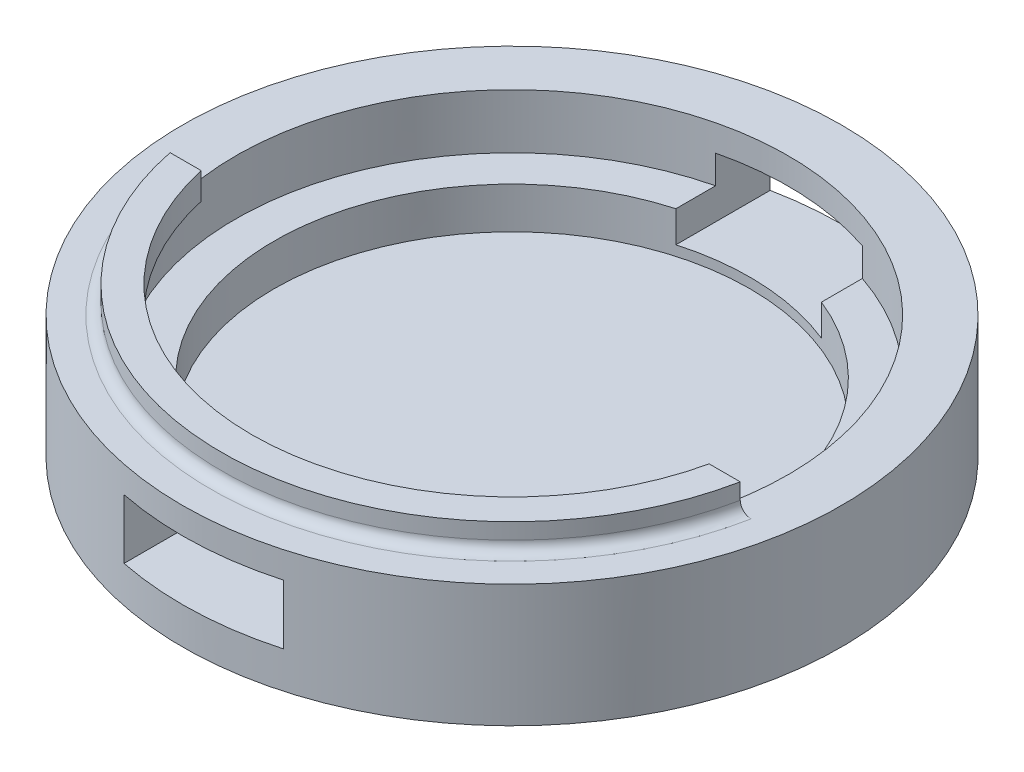
SolidWorks part; units mm, degrees
ref_plane "Alzado" through (0, 0, 0) normal (0, 0, 1) x (1, 0, 0)
ref_plane "Planta" through (0, 0, 0) normal (0, 1, 0) x (1, 0, 0)
ref_plane "Vista lateral" through (0, 0, 0) normal (1, 0, 0) x (0, 0, -1)
sketch "Croquis1" plane through (0, 0, 0) normal (0, 1, 0) x (1, 0, 0)
  circle A0 centre (0, 0) radius 51.815
  circle A1 centre (0, 0) radius 61.815
  dimension "D1" = 103.63
  dimension "D2" = 123.63
extrude "Saliente-Extruir2" add sketch "Croquis1" along normal blind 18
sketch "Croquis2" plane through (0, 18, 0) normal (0, 1, 0) x (1, 0, 0)
  line L0 (47.6484, -10.6642) -> (53.4742, -10.6642)
  line L1 (-53.4742, -10.6642) -> (-47.6484, -10.6642)
  arc A2 (-47.6484, -10.6642) -> (47.6484, -10.6642) centre (0, 0) ccw
  arc A3 (-53.4742, -10.6642) -> (53.4742, -10.6642) centre (0, 0) ccw
extrude "Saliente-Extruir4" add sketch "Croquis2" along normal blind 5
fillet "Redondeo2" radius 2 1 edges at (0, 18, 54.5272)
sketch "Croquis3" plane through (0, 0, 0) normal (0, -1, 0) x (1, 0, 0)
  circle A0 centre (0, 0) radius 61.815
extrude "Saliente-Extruir5" add sketch "Croquis3" along normal blind 5
sketch "Croquis4" plane through (0, -5, 0) normal (0, -1, 0) x (1, 0, 0)
  circle A0 centre (0, 55.6983) radius 3.5
  circle A1 centre (55.6983, 0) radius 3.5
  circle A2 centre (0, -55.6983) radius 3.5
  circle A3 centre (-55.6983, 0) radius 3.5
  point P11 (0, 0)
  dimension "D1" = 7
  dimension "D2" = 4
extrude "Cortar-Extruir1" cut sketch "Croquis4" against normal blind 5
sketch "Croquis5" plane through (0, -5, 0) normal (0, -1, 0) x (1, 0, 0)
  circle A0 centre (0, 55.6983) radius 3.5
  dimension "D1" = 55.6983
sketch "Croquis6" plane through (0, -5, 0) normal (0, -1, 0) x (1, 0, 0)
  arc A0 (-9.4545, -8.1769) -> (-8.1769, -9.4545) centre (0, 0) ccw
  spline S0 degree 3 poles (-10.111, 8.9914) (-14.9099, 15.405) (-3.1026, 26.7366) (26.6769, 28.6218) (9.3118, 18.3412) (8.6434, 12.2458) (8.9914, 10.111) knots 0.00619 0.00619 0.00619 0.00619 0.153841 0.345958 0.455748 0.513421 0.513421 0.513421 0.513421
  spline S1 degree 3 poles (8.9914, 10.111) (15.405, 14.9099) (26.7366, 3.1026) (28.6218, -26.6769) (18.3412, -9.3118) (12.2458, -8.6434) (10.111, -8.9914) knots 0.00619 0.00619 0.00619 0.00619 0.153841 0.345958 0.455748 0.513421 0.513421 0.513421 0.513421
  spline S2 degree 3 poles (10.111, -8.9914) (14.9099, -15.405) (3.1026, -26.7366) (-26.6769, -28.6218) (-9.3118, -18.3412) (-8.6434, -12.2458) (-8.9914, -10.111) knots 0.00619 0.00619 0.00619 0.00619 0.153841 0.345958 0.455748 0.513421 0.513421 0.513421 0.513421
  spline S3 degree 3 poles (-8.9914, -10.111) (-15.405, -14.9099) (-26.7366, -3.1026) (-28.6218, 26.6769) (-18.3412, 9.3118) (-12.2458, 8.6434) (-10.111, 8.9914) knots 0.00619 0.00619 0.00619 0.00619 0.153841 0.345958 0.455748 0.513421 0.513421 0.513421 0.513421
  point P25 (0, 0)
  dimension "D1" = 25
extrude "Cortar-Extruir2" cut sketch "Croquis6" against normal blind 3
sketch "Croquis7" plane through (0, -5, 0) normal (0, -1, 0) x (1, 0, 0)
  spline S14 degree 3 poles (340.8778, 2969.6757) (-144.0274, -413.7995) (-31.7257, 0.5508) (14.063, -10.1213) (14.3721, -10.2142) (14.9734, -10.4385) (15.2642, -10.5689) (15.8271, -10.8641) (16.0991, -11.0293) (16.6282, -11.3869) (16.8864, -11.5796) (17.6344, -12.1796) (18.1019, -12.6098) (19.4549, -13.9486) (20.2891, -14.907) (21.5423, -16.3427) (21.9597, -16.8217) (22.609, -17.5175) (22.8295, -17.7456) (23.2877, -18.1844) (23.5242, -18.3947) (24.0303, -18.7738) (24.3032, -18.9445) (24.7448, -19.1186) (24.8999, -19.1634) (25.2114, -19.2156) (25.3683, -19.2238) (25.6844, -19.1998) (25.8426, -19.1669) (26.1406, -19.0631) (26.2849, -18.9906) (26.6815, -18.7261) (26.9002, -18.4852) (27.2432, -17.9553) (27.3735, -17.6609) (27.5773, -17.0645) (27.6528, -16.7587) (27.7725, -16.1379) (27.8161, -15.8239) (27.8811, -15.1989) (27.9026, -14.8864) (27.9436, -13.9493) (27.94, -13.3248) (27.8935, -12.0761) (27.8501, -11.4519) (27.7324, -10.2038) (27.658, -9.5793) (27.4843, -8.3403) (27.3849, -7.7245) (27.0528, -5.8869) (26.787, -4.6749) (26.1706, -2.2757) (25.82, -1.0886) (25.0229, 1.2577) (24.5768, 2.4168) (23.8133, 4.1279) (23.5428, 4.6936) (22.9629, 5.8135) (22.6552, 6.3641) (21.9988, 7.4376) (21.6498, 7.9614) (20.8983, 8.9751) (20.4973, 9.4626) (19.6398, 10.376) (19.1824, 10.8036) (18.438, 11.3857) (18.1786, 11.5706) (17.6463, 11.9104) (17.3729, 12.0658) (16.8103, 12.3447) (16.5211, 12.4681) (15.9247, 12.6788) (15.6173, 12.7658) (14.695, 12.9611) (14.0708, 13.0077) (13.1203, 12.9496) (12.8053, 12.9089) (12.1872, 12.7898) (11.8826, 12.7113) (11.2815, 12.52) (10.984, 12.4066) (-24.7173, -3.2736) (39.5362, -229.2031) (-1376.9054, 2670.394) knots -2.259503 -2.259503 -2.259503 -2.259503 0.03125 0.03125 0.046875 0.046875 0.0625 0.0625 0.078125 0.078125 0.09375 0.09375 0.125 0.125 0.1875 0.1875 0.21875 0.21875 0.234375 0.234375 0.25 0.25 0.265625 0.265625 0.273437 0.273437 0.28125 0.28125 0.289062 0.289062 0.296875 0.296875 0.3125 0.3125 0.328125 0.328125 0.34375 0.34375 0.359375 0.359375 0.375 0.375 0.40625 0.40625 0.4375 0.4375 0.46875 0.46875 0.5 0.5 0.5625 0.5625 0.625 0.625 0.6875 0.6875 0.71875 0.71875 0.75 0.75 0.78125 0.78125 0.8125 0.8125 0.84375 0.84375 0.859375 0.859375 0.875 0.875 0.890625 0.890625 0.90625 0.90625 0.9375 0.9375 0.953125 0.953125 0.96875 0.96875 0.984375 0.984375 2.889942 2.889942 2.889942 2.889942 only from (11.8559, -9.8418) to (9.8418, 11.8559)
  spline S15 degree 3 poles (-2969.6829, 340.8787) (413.7996, -144.0274) (-0.5508, -31.7257) (10.1213, 14.063) (10.2142, 14.3721) (10.4385, 14.9734) (10.5689, 15.2642) (10.8641, 15.8271) (11.0293, 16.0991) (11.3869, 16.6282) (11.5796, 16.8864) (12.1796, 17.6344) (12.6098, 18.1019) (13.9486, 19.4549) (14.907, 20.2891) (16.3427, 21.5423) (16.8217, 21.9597) (17.5175, 22.609) (17.7456, 22.8295) (18.1844, 23.2877) (18.3947, 23.5242) (18.7738, 24.0303) (18.9445, 24.3032) (19.1186, 24.7448) (19.1634, 24.8999) (19.2156, 25.2114) (19.2238, 25.3683) (19.1998, 25.6844) (19.1669, 25.8426) (19.0631, 26.1406) (18.9906, 26.2849) (18.7261, 26.6815) (18.4852, 26.9002) (17.9553, 27.2432) (17.6609, 27.3735) (17.0645, 27.5773) (16.7587, 27.6528) (16.1379, 27.7725) (15.8239, 27.8161) (15.1989, 27.8811) (14.8864, 27.9026) (13.9493, 27.9436) (13.3248, 27.94) (12.0761, 27.8935) (11.4519, 27.8501) (10.2038, 27.7324) (9.5793, 27.658) (8.3403, 27.4843) (7.7245, 27.3849) (5.8869, 27.0528) (4.6749, 26.787) (2.2757, 26.1706) (1.0886, 25.82) (-1.2577, 25.0229) (-2.4168, 24.5768) (-4.1279, 23.8133) (-4.6936, 23.5428) (-5.8135, 22.9629) (-6.3641, 22.6552) (-7.4376, 21.9988) (-7.9614, 21.6498) (-8.9751, 20.8983) (-9.4626, 20.4973) (-10.376, 19.6398) (-10.8036, 19.1824) (-11.3857, 18.438) (-11.5706, 18.1786) (-11.9104, 17.6463) (-12.0658, 17.3729) (-12.3447, 16.8103) (-12.4681, 16.5211) (-12.6788, 15.9247) (-12.7658, 15.6173) (-12.9611, 14.695) (-13.0077, 14.0708) (-12.9496, 13.1203) (-12.9089, 12.8053) (-12.7898, 12.1872) (-12.7113, 11.8826) (-12.52, 11.2815) (-12.4066, 10.984) (3.2736, -24.7173) (229.2031, 39.5362) (-2670.3929, -1376.9044) knots -2.259503 -2.259503 -2.259503 -2.259503 0.03125 0.03125 0.046875 0.046875 0.0625 0.0625 0.078125 0.078125 0.09375 0.09375 0.125 0.125 0.1875 0.1875 0.21875 0.21875 0.234375 0.234375 0.25 0.25 0.265625 0.265625 0.273437 0.273437 0.28125 0.28125 0.289062 0.289062 0.296875 0.296875 0.3125 0.3125 0.328125 0.328125 0.34375 0.34375 0.359375 0.359375 0.375 0.375 0.40625 0.40625 0.4375 0.4375 0.46875 0.46875 0.5 0.5 0.5625 0.5625 0.625 0.625 0.6875 0.6875 0.71875 0.71875 0.75 0.75 0.78125 0.78125 0.8125 0.8125 0.84375 0.84375 0.859375 0.859375 0.875 0.875 0.890625 0.890625 0.90625 0.90625 0.9375 0.9375 0.953125 0.953125 0.96875 0.96875 0.984375 0.984375 2.889942 2.889942 2.889942 2.889942 only from (9.8418, 11.8559) to (-11.8559, 9.8418)
  spline S16 degree 3 poles (-340.8778, -2969.6757) (144.0274, 413.7995) (31.7257, -0.5508) (-14.063, 10.1213) (-14.3721, 10.2142) (-14.9734, 10.4385) (-15.2642, 10.5689) (-15.8271, 10.8641) (-16.0991, 11.0293) (-16.6282, 11.3869) (-16.8864, 11.5796) (-17.6344, 12.1796) (-18.1019, 12.6098) (-19.4549, 13.9486) (-20.2891, 14.907) (-21.5423, 16.3427) (-21.9597, 16.8217) (-22.609, 17.5175) (-22.8295, 17.7456) (-23.2877, 18.1844) (-23.5242, 18.3947) (-24.0303, 18.7738) (-24.3032, 18.9445) (-24.7448, 19.1186) (-24.8999, 19.1634) (-25.2114, 19.2156) (-25.3683, 19.2238) (-25.6844, 19.1998) (-25.8426, 19.1669) (-26.1406, 19.0631) (-26.2849, 18.9906) (-26.6815, 18.7261) (-26.9002, 18.4852) (-27.2432, 17.9553) (-27.3735, 17.6609) (-27.5773, 17.0645) (-27.6528, 16.7587) (-27.7725, 16.1379) (-27.8161, 15.8239) (-27.8811, 15.1989) (-27.9026, 14.8864) (-27.9436, 13.9493) (-27.94, 13.3248) (-27.8935, 12.0761) (-27.8501, 11.4519) (-27.7324, 10.2038) (-27.658, 9.5793) (-27.4843, 8.3403) (-27.3849, 7.7245) (-27.0528, 5.8869) (-26.787, 4.6749) (-26.1706, 2.2757) (-25.82, 1.0886) (-25.0229, -1.2577) (-24.5768, -2.4168) (-23.8133, -4.1279) (-23.5428, -4.6936) (-22.9629, -5.8135) (-22.6552, -6.3641) (-21.9988, -7.4376) (-21.6498, -7.9614) (-20.8983, -8.9751) (-20.4973, -9.4626) (-19.6398, -10.376) (-19.1824, -10.8036) (-18.438, -11.3857) (-18.1786, -11.5706) (-17.6463, -11.9104) (-17.3729, -12.0658) (-16.8103, -12.3447) (-16.5211, -12.4681) (-15.9247, -12.6788) (-15.6173, -12.7658) (-14.695, -12.9611) (-14.0708, -13.0077) (-13.1203, -12.9496) (-12.8053, -12.9089) (-12.1872, -12.7898) (-11.8826, -12.7113) (-11.2815, -12.52) (-10.984, -12.4066) (24.7173, 3.2736) (-39.5362, 229.2031) (1376.9054, -2670.3939) knots -2.259503 -2.259503 -2.259503 -2.259503 0.03125 0.03125 0.046875 0.046875 0.0625 0.0625 0.078125 0.078125 0.09375 0.09375 0.125 0.125 0.1875 0.1875 0.21875 0.21875 0.234375 0.234375 0.25 0.25 0.265625 0.265625 0.273437 0.273437 0.28125 0.28125 0.289062 0.289062 0.296875 0.296875 0.3125 0.3125 0.328125 0.328125 0.34375 0.34375 0.359375 0.359375 0.375 0.375 0.40625 0.40625 0.4375 0.4375 0.46875 0.46875 0.5 0.5 0.5625 0.5625 0.625 0.625 0.6875 0.6875 0.71875 0.71875 0.75 0.75 0.78125 0.78125 0.8125 0.8125 0.84375 0.84375 0.859375 0.859375 0.875 0.875 0.890625 0.890625 0.90625 0.90625 0.9375 0.9375 0.953125 0.953125 0.96875 0.96875 0.984375 0.984375 2.889942 2.889942 2.889942 2.889942 only from (-11.8559, 9.8418) to (-9.8418, -11.8559)
  spline S17 degree 3 poles (2969.6829, -340.8787) (-413.7996, 144.0274) (0.5508, 31.7257) (-10.1213, -14.063) (-10.2142, -14.3721) (-10.4385, -14.9734) (-10.5689, -15.2642) (-10.8641, -15.8271) (-11.0293, -16.0991) (-11.3869, -16.6282) (-11.5796, -16.8864) (-12.1796, -17.6344) (-12.6098, -18.1019) (-13.9486, -19.4549) (-14.907, -20.2891) (-16.3427, -21.5423) (-16.8217, -21.9597) (-17.5175, -22.609) (-17.7456, -22.8295) (-18.1844, -23.2877) (-18.3947, -23.5242) (-18.7738, -24.0303) (-18.9445, -24.3032) (-19.1186, -24.7448) (-19.1634, -24.8999) (-19.2156, -25.2114) (-19.2238, -25.3683) (-19.1998, -25.6844) (-19.1669, -25.8426) (-19.0631, -26.1406) (-18.9906, -26.2849) (-18.7261, -26.6815) (-18.4852, -26.9002) (-17.9553, -27.2432) (-17.6609, -27.3735) (-17.0645, -27.5773) (-16.7587, -27.6528) (-16.1379, -27.7725) (-15.8239, -27.8161) (-15.1989, -27.8811) (-14.8864, -27.9026) (-13.9493, -27.9436) (-13.3248, -27.94) (-12.0761, -27.8935) (-11.4519, -27.8501) (-10.2038, -27.7324) (-9.5793, -27.658) (-8.3403, -27.4843) (-7.7245, -27.3849) (-5.8869, -27.0528) (-4.6749, -26.787) (-2.2757, -26.1706) (-1.0886, -25.82) (1.2577, -25.0229) (2.4168, -24.5768) (4.1279, -23.8133) (4.6936, -23.5428) (5.8135, -22.9629) (6.3641, -22.6552) (7.4376, -21.9988) (7.9614, -21.6498) (8.9751, -20.8983) (9.4626, -20.4973) (10.376, -19.6398) (10.8036, -19.1824) (11.3857, -18.438) (11.5706, -18.1786) (11.9104, -17.6463) (12.0658, -17.3729) (12.3447, -16.8103) (12.4681, -16.5211) (12.6788, -15.9247) (12.7658, -15.6173) (12.9611, -14.695) (13.0077, -14.0708) (12.9496, -13.1203) (12.9089, -12.8053) (12.7898, -12.1872) (12.7113, -11.8826) (12.52, -11.2815) (12.4066, -10.984) (-3.2736, 24.7173) (-229.2031, -39.5362) (2670.393, 1376.9044) knots -2.259503 -2.259503 -2.259503 -2.259503 0.03125 0.03125 0.046875 0.046875 0.0625 0.0625 0.078125 0.078125 0.09375 0.09375 0.125 0.125 0.1875 0.1875 0.21875 0.21875 0.234375 0.234375 0.25 0.25 0.265625 0.265625 0.273437 0.273437 0.28125 0.28125 0.289062 0.289062 0.296875 0.296875 0.3125 0.3125 0.328125 0.328125 0.34375 0.34375 0.359375 0.359375 0.375 0.375 0.40625 0.40625 0.4375 0.4375 0.46875 0.46875 0.5 0.5 0.5625 0.5625 0.625 0.625 0.6875 0.6875 0.71875 0.71875 0.75 0.75 0.78125 0.78125 0.8125 0.8125 0.84375 0.84375 0.859375 0.859375 0.875 0.875 0.890625 0.890625 0.90625 0.90625 0.9375 0.9375 0.953125 0.953125 0.96875 0.96875 0.984375 0.984375 2.889942 2.889942 2.889942 2.889942 only from (-9.8418, -11.8559) to (11.8559, -9.8418)
  spline S18 degree 3 poles (11.8559, -9.8418) (12.4995, -9.8389) (13.1323, -9.9044) (14.063, -10.1213) (14.3721, -10.2142) (14.9734, -10.4385) (15.2642, -10.5689) (15.8271, -10.8641) (16.0991, -11.0293) (16.6282, -11.3869) (16.8864, -11.5796) (17.6344, -12.1796) (18.1019, -12.6098) (19.4549, -13.9486) (20.2891, -14.907) (21.5423, -16.3427) (21.9597, -16.8217) (22.609, -17.5175) (22.8295, -17.7456) (23.2877, -18.1844) (23.5242, -18.3947) (24.0303, -18.7738) (24.3032, -18.9445) (24.7448, -19.1186) (24.8999, -19.1634) (25.2114, -19.2156) (25.3683, -19.2238) (25.6844, -19.1998) (25.8426, -19.1669) (26.1406, -19.0631) (26.2849, -18.9906) (26.6815, -18.7261) (26.9002, -18.4852) (27.2432, -17.9553) (27.3735, -17.6609) (27.5773, -17.0645) (27.6528, -16.7587) (27.7725, -16.1379) (27.8161, -15.8239) (27.8811, -15.1989) (27.9026, -14.8864) (27.9436, -13.9493) (27.94, -13.3248) (27.8935, -12.0761) (27.8501, -11.4519) (27.7324, -10.2038) (27.658, -9.5793) (27.4843, -8.3403) (27.3849, -7.7245) (27.0528, -5.8869) (26.787, -4.6749) (26.1706, -2.2757) (25.82, -1.0886) (25.0229, 1.2577) (24.5768, 2.4168) (23.8133, 4.1279) (23.5428, 4.6936) (22.9629, 5.8135) (22.6552, 6.3641) (21.9988, 7.4376) (21.6498, 7.9614) (20.8983, 8.9751) (20.4973, 9.4626) (19.6398, 10.376) (19.1824, 10.8036) (18.438, 11.3857) (18.1786, 11.5706) (17.6463, 11.9104) (17.3729, 12.0658) (16.8103, 12.3447) (16.5211, 12.4681) (15.9247, 12.6788) (15.6173, 12.7658) (14.695, 12.9611) (14.0708, 13.0077) (13.1203, 12.9496) (12.8053, 12.9089) (12.1872, 12.7898) (11.8826, 12.7113) (11.2815, 12.52) (10.984, 12.4066) (10.4032, 12.1516) (10.1196, 12.0099) (9.8418, 11.8559) knots 0 0 0 0 0.03125 0.03125 0.046875 0.046875 0.0625 0.0625 0.078125 0.078125 0.09375 0.09375 0.125 0.125 0.1875 0.1875 0.21875 0.21875 0.234375 0.234375 0.25 0.25 0.265625 0.265625 0.273437 0.273437 0.28125 0.28125 0.289062 0.289062 0.296875 0.296875 0.3125 0.3125 0.328125 0.328125 0.34375 0.34375 0.359375 0.359375 0.375 0.375 0.40625 0.40625 0.4375 0.4375 0.46875 0.46875 0.5 0.5 0.5625 0.5625 0.625 0.625 0.6875 0.6875 0.71875 0.71875 0.75 0.75 0.78125 0.78125 0.8125 0.8125 0.84375 0.84375 0.859375 0.859375 0.875 0.875 0.890625 0.890625 0.90625 0.90625 0.9375 0.9375 0.953125 0.953125 0.96875 0.96875 0.984375 0.984375 1 1 1 1
  spline S19 degree 3 poles (9.8418, 11.8559) (9.8389, 12.4995) (9.9044, 13.1323) (10.1213, 14.063) (10.2142, 14.3721) (10.4385, 14.9734) (10.5689, 15.2642) (10.8641, 15.8271) (11.0293, 16.0991) (11.3869, 16.6282) (11.5796, 16.8864) (12.1796, 17.6344) (12.6098, 18.1019) (13.9486, 19.4549) (14.907, 20.2891) (16.3427, 21.5423) (16.8217, 21.9597) (17.5175, 22.609) (17.7456, 22.8295) (18.1844, 23.2877) (18.3947, 23.5242) (18.7738, 24.0303) (18.9445, 24.3032) (19.1186, 24.7448) (19.1634, 24.8999) (19.2156, 25.2114) (19.2238, 25.3683) (19.1998, 25.6844) (19.1669, 25.8426) (19.0631, 26.1406) (18.9906, 26.2849) (18.7261, 26.6815) (18.4852, 26.9002) (17.9553, 27.2432) (17.6609, 27.3735) (17.0645, 27.5773) (16.7587, 27.6528) (16.1379, 27.7725) (15.8239, 27.8161) (15.1989, 27.8811) (14.8864, 27.9026) (13.9493, 27.9436) (13.3248, 27.94) (12.0761, 27.8935) (11.4519, 27.8501) (10.2038, 27.7324) (9.5793, 27.658) (8.3403, 27.4843) (7.7245, 27.3849) (5.8869, 27.0528) (4.6749, 26.787) (2.2757, 26.1706) (1.0886, 25.82) (-1.2577, 25.0229) (-2.4168, 24.5768) (-4.1279, 23.8133) (-4.6936, 23.5428) (-5.8135, 22.9629) (-6.3641, 22.6552) (-7.4376, 21.9988) (-7.9614, 21.6498) (-8.9751, 20.8983) (-9.4626, 20.4973) (-10.376, 19.6398) (-10.8036, 19.1824) (-11.3857, 18.438) (-11.5706, 18.1786) (-11.9104, 17.6463) (-12.0658, 17.3729) (-12.3447, 16.8103) (-12.4681, 16.5211) (-12.6788, 15.9247) (-12.7658, 15.6173) (-12.9611, 14.695) (-13.0077, 14.0708) (-12.9496, 13.1203) (-12.9089, 12.8053) (-12.7898, 12.1872) (-12.7113, 11.8826) (-12.52, 11.2815) (-12.4066, 10.984) (-12.1516, 10.4032) (-12.0099, 10.1196) (-11.8559, 9.8418) knots 0 0 0 0 0.03125 0.03125 0.046875 0.046875 0.0625 0.0625 0.078125 0.078125 0.09375 0.09375 0.125 0.125 0.1875 0.1875 0.21875 0.21875 0.234375 0.234375 0.25 0.25 0.265625 0.265625 0.273437 0.273437 0.28125 0.28125 0.289062 0.289062 0.296875 0.296875 0.3125 0.3125 0.328125 0.328125 0.34375 0.34375 0.359375 0.359375 0.375 0.375 0.40625 0.40625 0.4375 0.4375 0.46875 0.46875 0.5 0.5 0.5625 0.5625 0.625 0.625 0.6875 0.6875 0.71875 0.71875 0.75 0.75 0.78125 0.78125 0.8125 0.8125 0.84375 0.84375 0.859375 0.859375 0.875 0.875 0.890625 0.890625 0.90625 0.90625 0.9375 0.9375 0.953125 0.953125 0.96875 0.96875 0.984375 0.984375 1 1 1 1
  spline S20 degree 3 poles (-11.8559, 9.8418) (-12.4995, 9.8389) (-13.1323, 9.9044) (-14.063, 10.1213) (-14.3721, 10.2142) (-14.9734, 10.4385) (-15.2642, 10.5689) (-15.8271, 10.8641) (-16.0991, 11.0293) (-16.6282, 11.3869) (-16.8864, 11.5796) (-17.6344, 12.1796) (-18.1019, 12.6098) (-19.4549, 13.9486) (-20.2891, 14.907) (-21.5423, 16.3427) (-21.9597, 16.8217) (-22.609, 17.5175) (-22.8295, 17.7456) (-23.2877, 18.1844) (-23.5242, 18.3947) (-24.0303, 18.7738) (-24.3032, 18.9445) (-24.7448, 19.1186) (-24.8999, 19.1634) (-25.2114, 19.2156) (-25.3683, 19.2238) (-25.6844, 19.1998) (-25.8426, 19.1669) (-26.1406, 19.0631) (-26.2849, 18.9906) (-26.6815, 18.7261) (-26.9002, 18.4852) (-27.2432, 17.9553) (-27.3735, 17.6609) (-27.5773, 17.0645) (-27.6528, 16.7587) (-27.7725, 16.1379) (-27.8161, 15.8239) (-27.8811, 15.1989) (-27.9026, 14.8864) (-27.9436, 13.9493) (-27.94, 13.3248) (-27.8935, 12.0761) (-27.8501, 11.4519) (-27.7324, 10.2038) (-27.658, 9.5793) (-27.4843, 8.3403) (-27.3849, 7.7245) (-27.0528, 5.8869) (-26.787, 4.6749) (-26.1706, 2.2757) (-25.82, 1.0886) (-25.0229, -1.2577) (-24.5768, -2.4168) (-23.8133, -4.1279) (-23.5428, -4.6936) (-22.9629, -5.8135) (-22.6552, -6.3641) (-21.9988, -7.4376) (-21.6498, -7.9614) (-20.8983, -8.9751) (-20.4973, -9.4626) (-19.6398, -10.376) (-19.1824, -10.8036) (-18.438, -11.3857) (-18.1786, -11.5706) (-17.6463, -11.9104) (-17.3729, -12.0658) (-16.8103, -12.3447) (-16.5211, -12.4681) (-15.9247, -12.6788) (-15.6173, -12.7658) (-14.695, -12.9611) (-14.0708, -13.0077) (-13.1203, -12.9496) (-12.8053, -12.9089) (-12.1872, -12.7898) (-11.8826, -12.7113) (-11.2815, -12.52) (-10.984, -12.4066) (-10.4032, -12.1516) (-10.1196, -12.0099) (-9.8418, -11.8559) knots 0 0 0 0 0.03125 0.03125 0.046875 0.046875 0.0625 0.0625 0.078125 0.078125 0.09375 0.09375 0.125 0.125 0.1875 0.1875 0.21875 0.21875 0.234375 0.234375 0.25 0.25 0.265625 0.265625 0.273437 0.273437 0.28125 0.28125 0.289062 0.289062 0.296875 0.296875 0.3125 0.3125 0.328125 0.328125 0.34375 0.34375 0.359375 0.359375 0.375 0.375 0.40625 0.40625 0.4375 0.4375 0.46875 0.46875 0.5 0.5 0.5625 0.5625 0.625 0.625 0.6875 0.6875 0.71875 0.71875 0.75 0.75 0.78125 0.78125 0.8125 0.8125 0.84375 0.84375 0.859375 0.859375 0.875 0.875 0.890625 0.890625 0.90625 0.90625 0.9375 0.9375 0.953125 0.953125 0.96875 0.96875 0.984375 0.984375 1 1 1 1
  spline S21 degree 3 poles (-9.8418, -11.8559) (-9.8389, -12.4995) (-9.9044, -13.1323) (-10.1213, -14.063) (-10.2142, -14.3721) (-10.4385, -14.9734) (-10.5689, -15.2642) (-10.8641, -15.8271) (-11.0293, -16.0991) (-11.3869, -16.6282) (-11.5796, -16.8864) (-12.1796, -17.6344) (-12.6098, -18.1019) (-13.9486, -19.4549) (-14.907, -20.2891) (-16.3427, -21.5423) (-16.8217, -21.9597) (-17.5175, -22.609) (-17.7456, -22.8295) (-18.1844, -23.2877) (-18.3947, -23.5242) (-18.7738, -24.0303) (-18.9445, -24.3032) (-19.1186, -24.7448) (-19.1634, -24.8999) (-19.2156, -25.2114) (-19.2238, -25.3683) (-19.1998, -25.6844) (-19.1669, -25.8426) (-19.0631, -26.1406) (-18.9906, -26.2849) (-18.7261, -26.6815) (-18.4852, -26.9002) (-17.9553, -27.2432) (-17.6609, -27.3735) (-17.0645, -27.5773) (-16.7587, -27.6528) (-16.1379, -27.7725) (-15.8239, -27.8161) (-15.1989, -27.8811) (-14.8864, -27.9026) (-13.9493, -27.9436) (-13.3248, -27.94) (-12.0761, -27.8935) (-11.4519, -27.8501) (-10.2038, -27.7324) (-9.5793, -27.658) (-8.3403, -27.4843) (-7.7245, -27.3849) (-5.8869, -27.0528) (-4.6749, -26.787) (-2.2757, -26.1706) (-1.0886, -25.82) (1.2577, -25.0229) (2.4168, -24.5768) (4.1279, -23.8133) (4.6936, -23.5428) (5.8135, -22.9629) (6.3641, -22.6552) (7.4376, -21.9988) (7.9614, -21.6498) (8.9751, -20.8983) (9.4626, -20.4973) (10.376, -19.6398) (10.8036, -19.1824) (11.3857, -18.438) (11.5706, -18.1786) (11.9104, -17.6463) (12.0658, -17.3729) (12.3447, -16.8103) (12.4681, -16.5211) (12.6788, -15.9247) (12.7658, -15.6173) (12.9611, -14.695) (13.0077, -14.0708) (12.9496, -13.1203) (12.9089, -12.8053) (12.7898, -12.1872) (12.7113, -11.8826) (12.52, -11.2815) (12.4066, -10.984) (12.1516, -10.4032) (12.0099, -10.1196) (11.8559, -9.8418) knots 0 0 0 0 0.03125 0.03125 0.046875 0.046875 0.0625 0.0625 0.078125 0.078125 0.09375 0.09375 0.125 0.125 0.1875 0.1875 0.21875 0.21875 0.234375 0.234375 0.25 0.25 0.265625 0.265625 0.273437 0.273437 0.28125 0.28125 0.289062 0.289062 0.296875 0.296875 0.3125 0.3125 0.328125 0.328125 0.34375 0.34375 0.359375 0.359375 0.375 0.375 0.40625 0.40625 0.4375 0.4375 0.46875 0.46875 0.5 0.5 0.5625 0.5625 0.625 0.625 0.6875 0.6875 0.71875 0.71875 0.75 0.75 0.78125 0.78125 0.8125 0.8125 0.84375 0.84375 0.859375 0.859375 0.875 0.875 0.890625 0.890625 0.90625 0.90625 0.9375 0.9375 0.953125 0.953125 0.96875 0.96875 0.984375 0.984375 1 1 1 1
  dimension "D2" = 1
extrude "Cortar-Extruir3" cut sketch "Croquis7" against normal blind 3
sketch "Croquis8" plane through (0, 0, 0) normal (0, 0, 1) x (1, 0, 0)
  line L1 (-6.9026, 3.9196) -> (9.7448, 3.9196)
  line L2 (-6.9026, 3.9196) -> (-6.9026, -1.7649)
  line L3 (-6.9026, -1.7649) -> (9.7448, -1.7649)
  line L4 (9.7448, 3.9196) -> (9.7448, -1.7649)
sketch "Croquis10" plane through (0, 0, 0) normal (0, 0, 1) x (1, 0, 0)
  line L0 (51.815, 18) -> (51.815, 7.75) construction
  line L2 (51.815, 18) -> (-51.815, 18) construction
  line L4 (51.815, 7.75) -> (44.6185, 7.75)
  line L5 (51.815, 7.75) -> (51.815, 0)
  line L6 (51.815, 0) -> (44.6185, 0)
  line L7 (44.6185, 7.75) -> (44.6185, 0)
  dimension "D1" = 7.1965
sweep "Barrer2" add profiles "Croquis10" path edge at (0, 0, 51.815)
sketch "Croquis15" plane through (0, 0, 0) normal (0, 0, 1) x (1, 0, 0)
  line L0 (-12.181, 1.8851) -> (16.6474, 1.8851)
  line L5 (-12.181, 13.0553) -> (16.6474, 13.0553)
  line L6 (-12.181, 13.0553) -> (-12.181, 1.8851)
  line L8 (16.6474, 13.0553) -> (16.6474, 1.8851)
extrude "Cortar-Extruir4" cut sketch "Croquis15" against normal through all both and the other way through all
